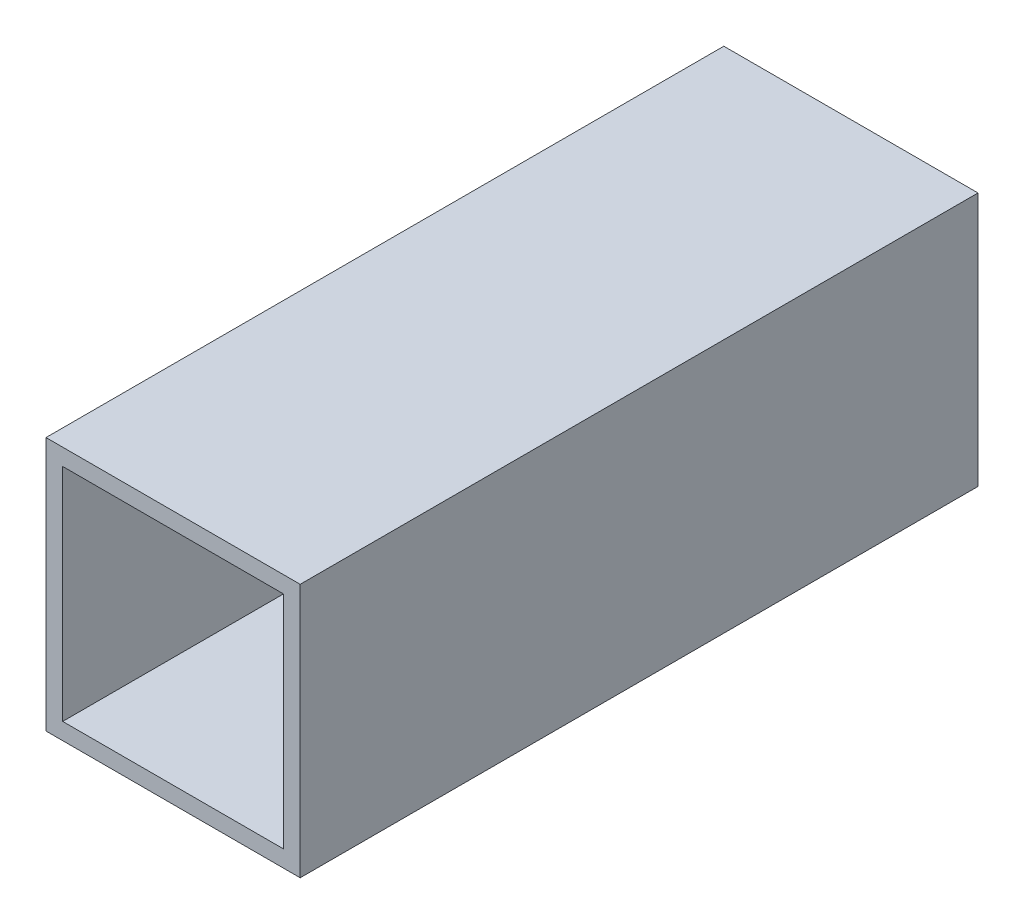
SolidWorks part; units mm, degrees
ref_plane "Front Plane" through (0, 0, 0) normal (0, 0, 1) x (1, 0, 0)
ref_plane "Top Plane" through (0, 0, 0) normal (0, 1, 0) x (1, 0, 0)
ref_plane "Right Plane" through (0, 0, 0) normal (1, 0, 0) x (0, 0, -1)
sketch "Sketch1" plane through (0, 0, 0) normal (0, 0, 1) x (1, 0, 0)
  line L0 (-33.1, 33.1) -> (33.1, 33.1)
  line L1 (-38.1, -38.1) -> (38.1, -38.1)
  line L2 (-38.1, -38.1) -> (-38.1, 38.1)
  line L3 (-38.1, 38.1) -> (38.1, 38.1)
  line L4 (38.1, -38.1) -> (38.1, 38.1)
  line L5 (-38.1, -38.1) -> (38.1, 38.1) construction
  line L6 (-38.1, 38.1) -> (38.1, -38.1) construction
  line L7 (33.1, -33.1) -> (33.1, 33.1)
  line L8 (-33.1, -33.1) -> (33.1, -33.1)
  line L9 (-33.1, -33.1) -> (-33.1, 33.1)
  point P0 (0, 0)
  dimension "D1" = 76.2
  dimension "D2" = 76.2
  dimension "D3" = 5
extrude "Boss-Extrude1" add sketch "Sketch1" along normal blind 203.2
